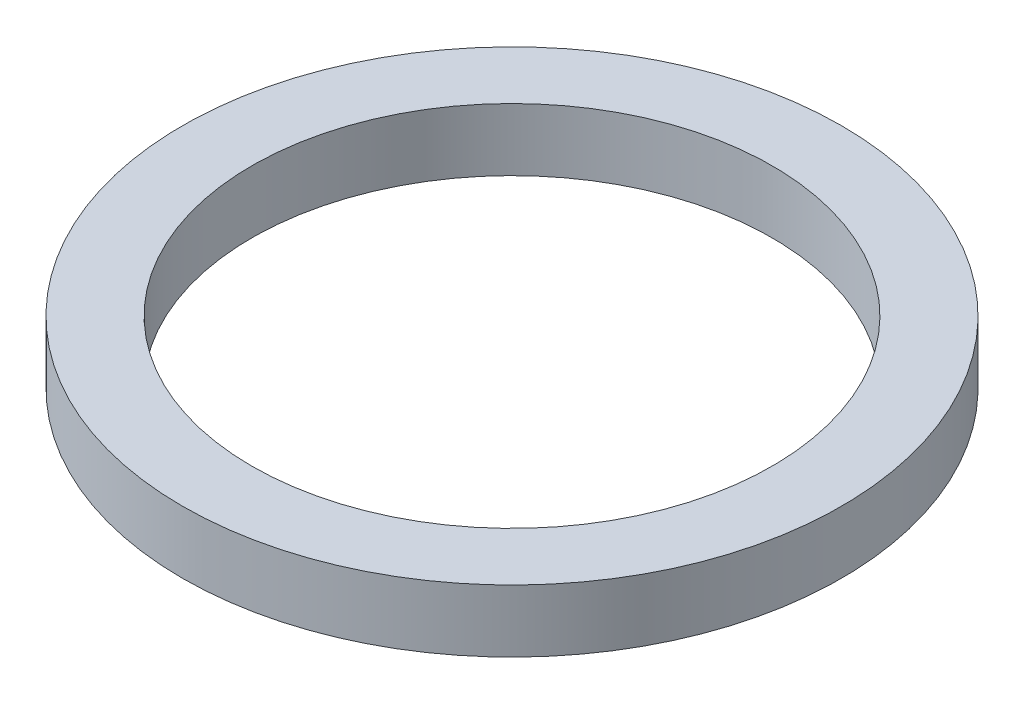
SolidWorks part; units mm, degrees
ref_plane "Front Plane" through (0, 0, 0) normal (0, 0, 1) x (1, 0, 0)
ref_plane "Top Plane" through (0, 0, 0) normal (0, 1, 0) x (1, 0, 0)
ref_plane "Right Plane" through (0, 0, 0) normal (1, 0, 0) x (0, 0, -1)
sketch "Sketch1" plane through (0, 0, 0) normal (0, 1, 0) x (1, 0, 0)
  circle A0 centre (0, 0) radius 37.5
  circle A1 centre (0, 0) radius 47.5
  dimension "D1" = 75
  dimension "D2" = 95
extrude "Boss-Extrude1" add sketch "Sketch1" along normal blind 9
